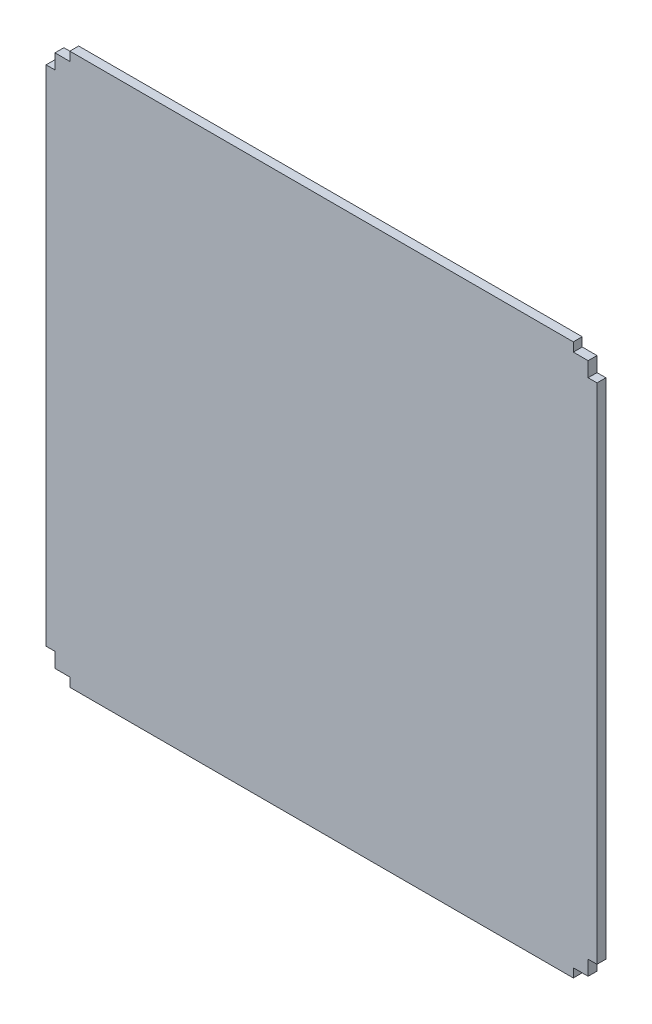
SolidWorks part; units mm, degrees
ref_plane "前视基准面" through (0, 0, 0) normal (0, 0, 1) x (1, 0, 0)
ref_plane "上视基准面" through (0, 0, 0) normal (0, 1, 0) x (1, 0, 0)
ref_plane "右视基准面" through (0, 0, 0) normal (1, 0, 0) x (0, 0, -1)
sketch "草图1" plane through (0, 0, 0) normal (0, 0, 1) x (1, 0, 0)
  line L0 (0, 180) -> (0, 175)
  line L1 (0, 0) -> (5, 0)
  line L2 (0, 0) -> (0, 5)
  line L3 (0, 180) -> (5, 180)
  line L4 (180, 0) -> (180, 5)
  line L5 (0, 175) -> (-3, 175)
  line L7 (0, 5) -> (-3, 5)
  line L8 (-3, 5) -> (-3, 175)
  line L11 (5, 0) -> (5, -3)
  line L12 (5, -3) -> (175, -3)
  line L13 (175, -3) -> (175, 0)
  line L15 (180, 5) -> (183, 5)
  line L16 (183, 5) -> (183, 175)
  line L17 (183, 175) -> (180, 175)
  line L18 (180, 180) -> (175, 180)
  line L19 (175, 180) -> (175, 183)
  line L20 (175, 183) -> (5, 183)
  line L21 (5, 183) -> (5, 180)
  line L23 (180, 175) -> (180, 180)
  line L24 (175, 0) -> (180, 0)
extrude "凸台-拉伸1" add sketch "草图1" along normal blind 3
